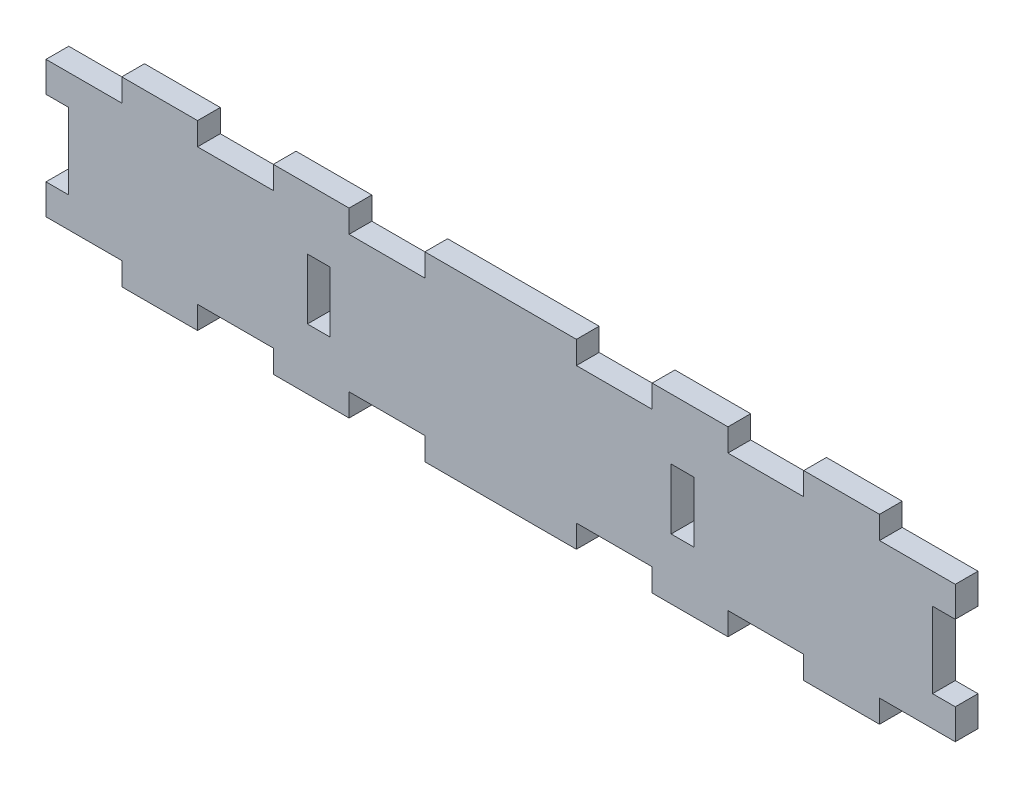
SolidWorks part; units mm, degrees
material "PC High Viscosity"
ref_plane "Front Plane" through (0, 0, 0) normal (0, 0, 1) x (1, 0, 0)
ref_plane "Top Plane" through (0, 0, 0) normal (0, 1, 0) x (1, 0, 0)
ref_plane "Right Plane" through (0, 0, 0) normal (1, 0, 0) x (0, 0, -1)
sketch "Sketch1" plane through (0, 0, 0) normal (0, 0, 1) x (1, 0, 0)
  line L1 (-60, -12) -> (60, -12)
  line L2 (-60, -12) -> (-60, 12)
  line L3 (-60, 12) -> (60, 12)
  line L4 (60, -12) -> (60, 12)
  line L5 (-60, -12) -> (60, 12) construction
  line L6 (-60, 12) -> (60, -12) construction
  point P0 (0, 0)
  dimension "D1" = 120
  dimension "D2" = 24
extrude "Boss-Extrude1" add sketch "Sketch1" along normal blind 3
sketch "Sketch2" plane through (0, 0, 3) normal (0, 0, 1) x (1, 0, 0)
  line L0 (60, -12) -> (60, 12) construction
  line L1 (60, 12) -> (-60, 12) construction
  line L3 (20, 12) -> (30, 12) construction
  line L4 (10, 12) -> (20, 12)
  line L5 (10, 12) -> (10, 9)
  line L6 (10, 9) -> (20, 9)
  line L7 (20, 12) -> (20, 9)
  line L8 (30, 12) -> (40, 12)
  line L9 (30, 12) -> (30, 9)
  line L10 (30, 9) -> (40, 9)
  line L11 (40, 12) -> (40, 9)
  line L12 (50, 12) -> (60, 12)
  line L13 (50, 12) -> (50, 9)
  line L14 (50, 9) -> (60, 9)
  line L15 (60, 12) -> (60, 9)
  line L16 (40, 12) -> (50, 12) construction
  dimension "D1" = 10
  dimension "D2" = 3
extrude "Cut-Extrude1" cut sketch "Sketch2" against normal through all
mirror "Mirror2" about plane through (0, 0, 0) normal (1, 0, 0) of "Cut-Extrude1"
mirror "Mirror3" about plane through (0, 0, 0) normal (0, 1, 0) of "Mirror2", "Cut-Extrude1"
sketch "Sketch3" plane through (0, 0, 3) normal (0, 0, 1) x (1, 0, 0)
  line L0 (0, -12) -> (0, 12) construction
  line L1 (-10, -12) -> (10, -12) construction
  line L2 (10, 12) -> (-10, 12) construction
  line L3 (60, 0) -> (-60, 0) construction
  line L4 (22.5, 4) -> (25.5, 4)
  line L5 (22.5, 4) -> (22.5, -4)
  line L6 (22.5, -4) -> (25.5, -4)
  line L7 (25.5, 4) -> (25.5, -4)
  line L8 (60, -9) -> (60, 9) construction
  line L9 (-60, 9) -> (-60, -9) construction
  line L10 (-25.5, 4) -> (-25.5, -4)
  line L11 (-22.5, -4) -> (-25.5, -4)
  line L12 (-22.5, 4) -> (-22.5, -4)
  line L13 (-22.5, 4) -> (-25.5, 4)
  line L14 (57, 5) -> (57, -5)
  line L15 (-60, 5) -> (-57, 5)
  line L16 (-60, 5) -> (-60, -5)
  line L17 (-60, -5) -> (-57, -5)
  line L18 (-57, 5) -> (-57, -5)
  line L19 (60, -5) -> (57, -5)
  line L20 (60, 5) -> (60, -5)
  line L21 (60, 5) -> (57, 5)
  dimension "D1" = 3
  dimension "D2" = 8
  dimension "D3" = 45
  dimension "D4" = 10
extrude "Cut-Extrude2" cut sketch "Sketch3" against normal through all
equation "\"pulley_pitch_diam\"= 12.73mm"
equation "\"pulley_total_width\"= 16mm"
equation "\"pulley_total_diam\"= 16mm"
equation "\"belt_width\"= 6mm"
equation "\"material_thickness\"= 3mm"
equation "\"shaft_diam\"= 8mm"
equation "\"bearing_od\"= 22mm"
equation "\"bearing_thickness\"= 7mm"
equation "\"D1@Boss-Extrude1\"=\"material_thickness\""
equation "\"D2@Sketch2\"=\"material_thickness\""
equation "\"D1@Sketch3\"=\"material_thickness\""
